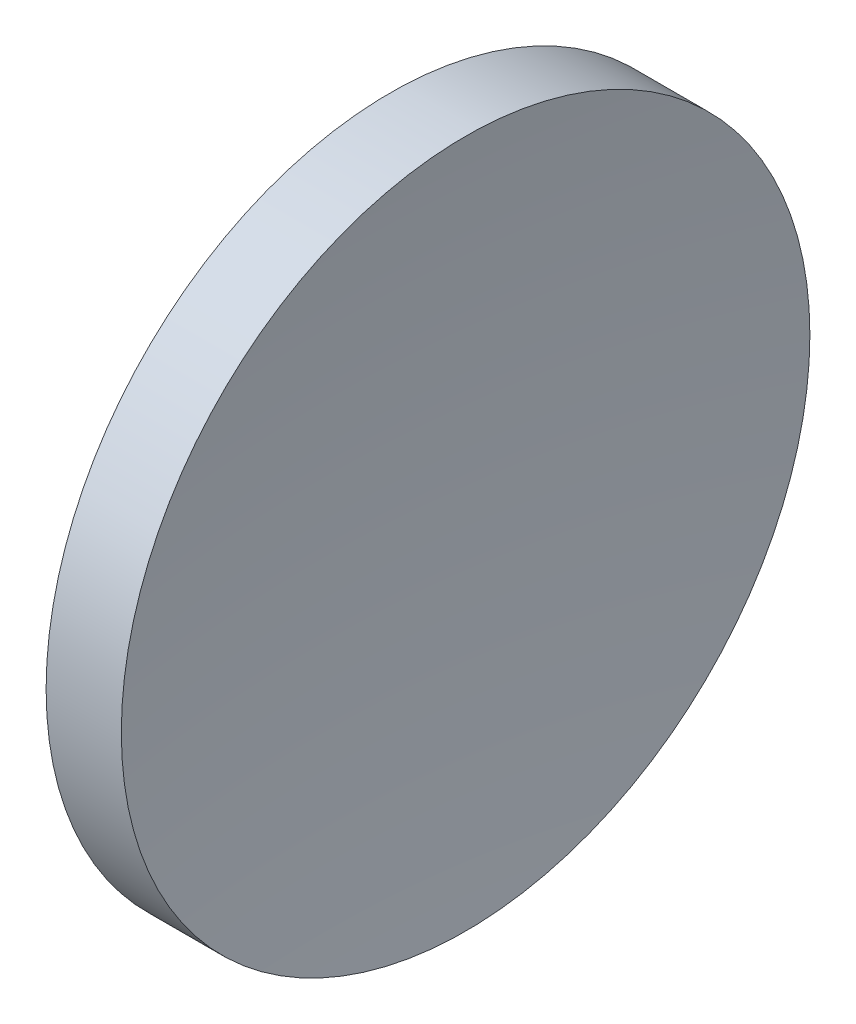
SolidWorks part; units mm, degrees
ref_plane "前视基准面" through (0, 0, 0) normal (0, 0, 1) x (1, 0, 0)
ref_plane "上视基准面" through (0, 0, 0) normal (0, 1, 0) x (1, 0, 0)
ref_plane "右视基准面" through (0, 0, 0) normal (1, 0, 0) x (0, 0, -1)
sketch "草图1" plane through (0, 0, 0) normal (0, 0, 1) x (1, 0, 0)
  line L0 (111.9552, 71.194) -> (137.836, 71.194) construction
  line L1 (119.5068, 71.194) -> (119.5068, 83.894)
  line L2 (119.5068, 83.894) -> (122.2811, 83.894)
  line L3 (121.5068, 71.194) -> (119.5068, 71.194)
  arc A0 (122.2811, 83.894) -> (121.5068, 71.194) centre (226.7068, 71.1542) ccw
revolve "旋转1" add sketch "草图1" angle 360 about L0
